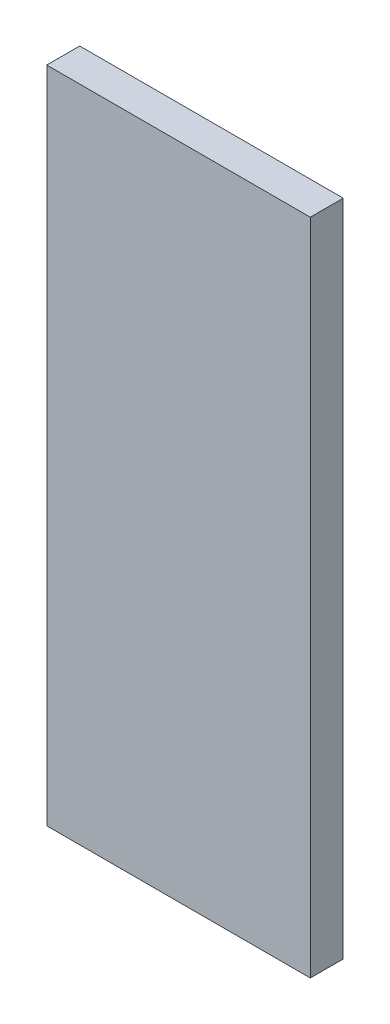
SolidWorks part; units mm, degrees
ref_plane "Alzado" through (0, 0, 0) normal (0, 0, 1) x (1, 0, 0)
ref_plane "Planta" through (0, 0, 0) normal (0, 1, 0) x (1, 0, 0)
ref_plane "Vista lateral" through (0, 0, 0) normal (1, 0, 0) x (0, 0, -1)
sketch "Croquis1" plane through (0, 0, 0) normal (0, 0, 1) x (1, 0, 0)
  line L0 (0, 0) -> (0, 50)
  line L1 (0, 50) -> (20, 50)
  line L2 (20, 50) -> (20, 0)
  line L3 (20, 0) -> (0, 0)
  dimension "D1" = 20
  dimension "D2" = 50
extrude "Saliente-Extruir1" add sketch "Croquis1" along normal blind 2.5
